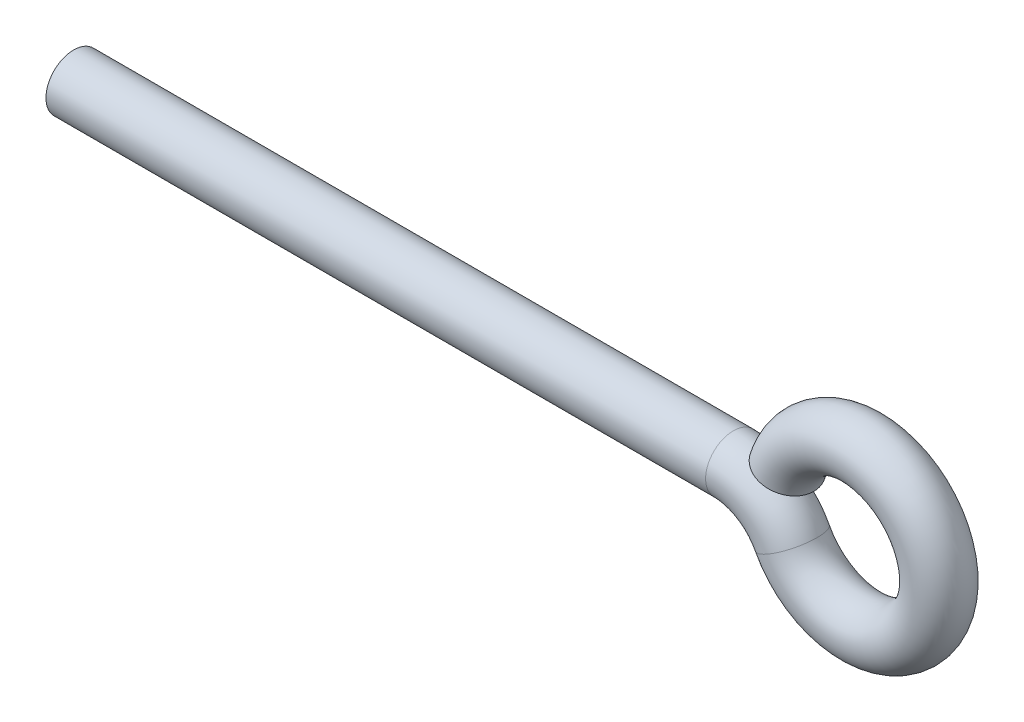
SolidWorks part; units mm, degrees
ref_plane "Piano frontale" through (0, 0, 0) normal (0, 0, 1) x (1, 0, 0)
ref_plane "Piano superiore" through (0, 0, 0) normal (0, 1, 0) x (1, 0, 0)
ref_plane "Piano destro" through (0, 0, 0) normal (1, 0, 0) x (0, 0, -1)
sketch "Schizzo1" plane through (0, 0, 0) normal (0, 0, 1) x (1, 0, 0)
  line L0 (0, 10.5836) -> (0, -21.3891) construction
  line L1 (-31.5978, 0) -> (-9.5, 0) construction
  line L2 (-41.5, 0) -> (-11.7663, 0)
  line L3 (-6, 0) -> (-12.3831, 2.074) construction
  arc A1 (-9.1049, -1.6154) -> (-9.3287, 1.0816) centre (-6, 0) ccw
  arc A2 (-9.1049, -1.6154) -> (-11.7663, 0) centre (-11.7663, -3) ccw
  dimension "D1" = 7
  dimension "D4" = 3
  dimension "D2" = 6
  dimension "20" = 32
  dimension "D3" = 18
sweep "Sweep1" add path "Schizzo1" circular profile diameter 2.5 parameters "D3"=2.5
sketch "Schizzo10" plane through (0, 0, 0) normal (0, 0, 1) x (1, 0, 0)
  line L0 (0, 0) -> (-43.6618, 0) construction
  circle A0 centre (-4.5, 0) radius 0.5
  dimension "D1" = 1
  dimension "D2" = 4.5
